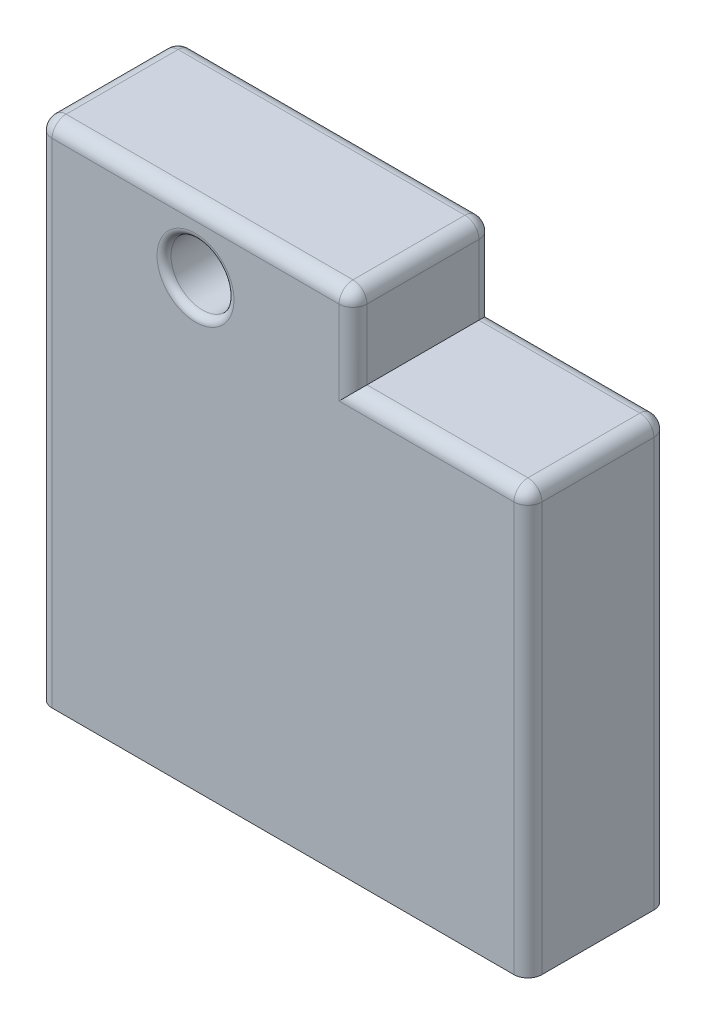
SolidWorks part; units mm, degrees
ref_plane "Front Plane" through (0, 0, 0) normal (0, 0, 1) x (1, 0, 0)
ref_plane "Top Plane" through (0, 0, 0) normal (0, 1, 0) x (1, 0, 0)
ref_plane "Right Plane" through (0, 0, 0) normal (1, 0, 0) x (0, 0, -1)
sketch "Sketch2" plane through (0, 0, 0) normal (0, 0, 1) x (1, 0, 0)
  line L0 (0, 0) -> (0, 92.075)
  line L1 (0, 92.075) -> (18.075, 92.075)
  line L2 (88.9, 76.835) -> (88.9, 0)
  line L3 (88.9, 0) -> (0, 0)
  line L4 (38.575, 92.075) -> (57.15, 92.075)
  line L7 (57.15, 92.075) -> (57.15, 76.835)
  line L9 (57.15, 76.835) -> (88.9, 76.835)
  line L10 (18.075, 92.075) -> (38.575, 92.075)
  point P4 (0, 0)
  point P10 (57.15, 92.075)
  point P12 (28.325, 81.825)
  dimension "D3" = 10.25
  dimension "D1" = 92.075
  dimension "D2" = 88.9
  dimension "D5" = 57.15
extrude "Boss-Extrude1" add sketch "Sketch2" along normal blind 25.4
sketch "Sketch9" plane through (0, 0, 25.4) normal (0, 0, 1) x (1, 0, 0)
  line L0 (57.15, 92.075) -> (0, 92.075) construction
  circle A0 centre (28.5664, 80.645) radius 5.715
  point P0 (28.5664, 80.645)
  dimension "D2" = 11.43
  dimension "D1" = 11.43
extrude "Cut-Extrude1" cut sketch "Sketch9" against normal through all
fillet "Fillet9" radius 2.54 13 edges at (28.575, 92.075, 25.4) (0, 46.0375, 25.4) (0, 46.0375, 0) (88.9, 38.4175, 0) (88.9, 38.4175, 25.4) (88.9, 76.835, 12.7) (73.025, 76.835, 25.4) (57.15, 84.455, 25.4) (57.15, 84.455, 0) (73.025, 76.835, 0) (28.575, 92.075, 0) (0, 92.075, 12.7) (57.15, 92.075, 12.7)
fillet "Fillet10" radius 1.27 2 edges at (34.2814, 80.645, 25.4) (34.2814, 80.645, 0)
